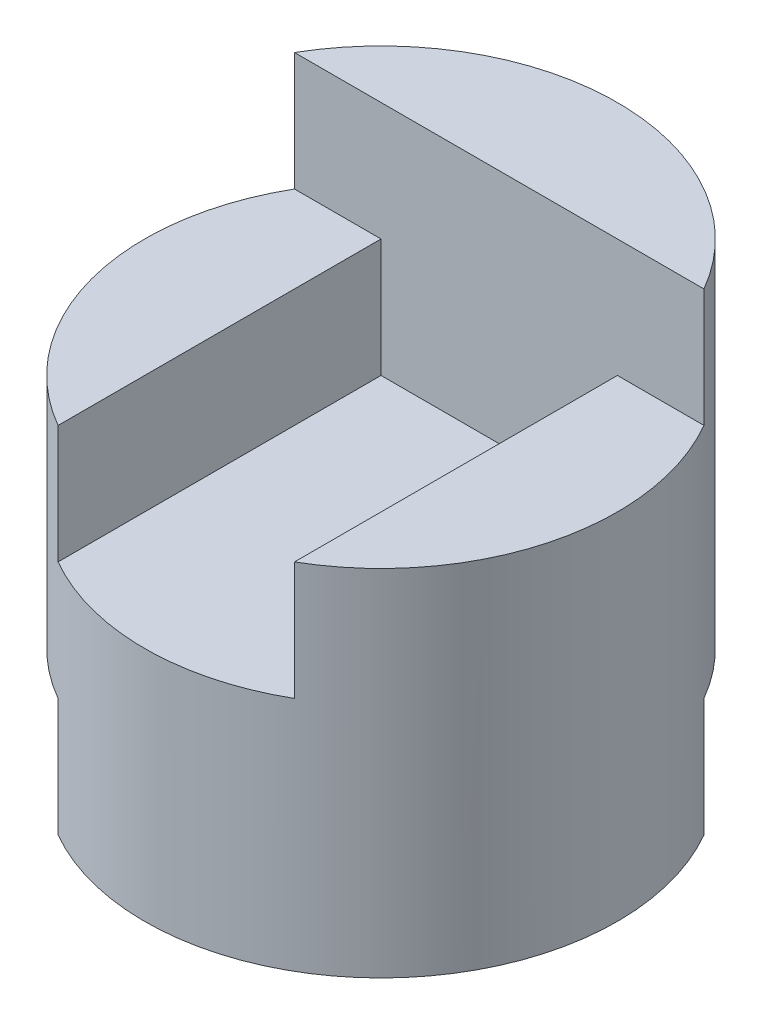
SolidWorks part; units mm, degrees
ref_plane "Front" through (0, 0, 0) normal (0, 0, 1) x (1, 0, 0)
ref_plane "Top" through (0, 0, 0) normal (0, 1, 0) x (1, 0, 0)
ref_plane "Right" through (0, 0, 0) normal (1, 0, 0) x (0, 0, -1)
sketch "Sketch1" plane through (0, 0, 0) normal (0, 1, 0) x (1, 0, 0)
  circle A0 centre (0, 0) radius 2
  dimension "D1" = 4
extrude "Boss-Extrude1" add sketch "Sketch1" along normal blind 4
sketch "Sketch2" plane through (0, 0, 0) normal (0, 0, 1) x (1, 0, 0)
  line L0 (-2, 4) -> (2, 4)
  line L1 (2, 4) -> (2, 3)
  line L2 (2, 0) -> (2, 4) construction
  line L3 (2, 3) -> (1, 3)
  line L4 (1, 3) -> (1, 2)
  line L5 (1, 2) -> (-1, 2)
  line L6 (-1, 2) -> (-1, 3)
  line L7 (-1, 3) -> (-2, 3)
  line L8 (-2, 4) -> (-2, 0) construction
  line L9 (-2, 3) -> (-2, 4)
  line L11 (-2, 0) -> (-1, 0)
  line L12 (-2, 0) -> (-2, 1)
  line L13 (-2, 1) -> (-1, 1)
  line L14 (-1, 0) -> (-1, 1)
  dimension "D1" = 1
  dimension "D2" = 1
  dimension "D3" = 1
  dimension "D4" = 1
  dimension "D5" = 2
  dimension "D6" = 1
  dimension "D7" = 1
extrude "Cut-Extrude4" cut sketch "Sketch2" against normal blind 1 and the other way blind 11
sketch "Sketch5" plane through (0, 0, 0) normal (1, 0, 0) x (0, 0, -1)
  line L1 (1, 1) -> (2, 1)
  line L2 (1, 1) -> (1, 0)
  line L3 (1, 0) -> (2, 0)
  line L4 (2, 1) -> (2, 0)
extrude "Cut-Extrude5" cut sketch "Sketch5" against normal mid plane 11
